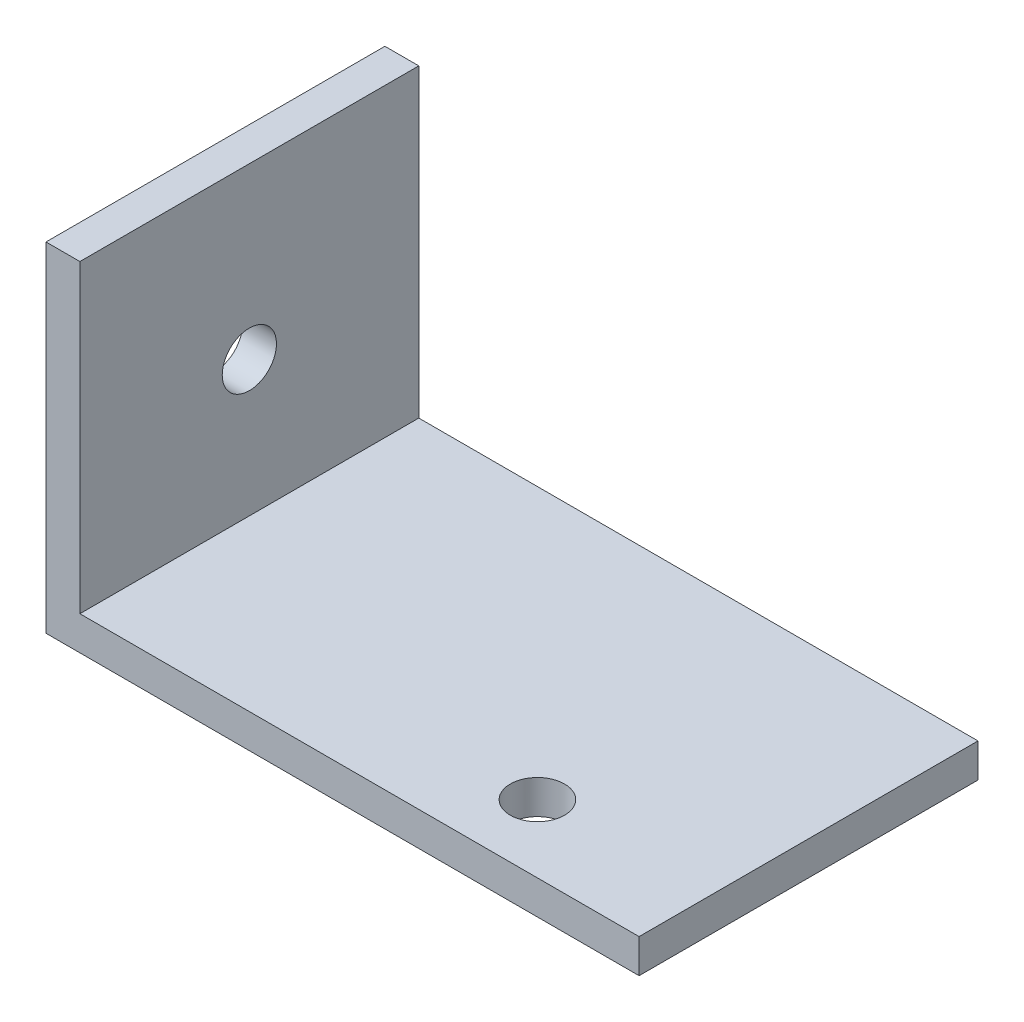
SolidWorks part; units mm, degrees
material "1060 Сплав"
ref_plane "Спереди" through (0, 0, 0) normal (0, 0, 1) x (1, 0, 0)
ref_plane "Сверху" through (0, 0, 0) normal (0, 1, 0) x (1, 0, 0)
ref_plane "Справа" through (0, 0, 0) normal (1, 0, 0) x (0, 0, -1)
sketch "Эскиз1" plane through (0, 0, 0) normal (0, 0, 1) x (1, 0, 0)
  line L0 (0, 0) -> (35, 0)
  line L1 (35, 0) -> (35, 2)
  line L2 (35, 2) -> (2, 2)
  line L3 (2, 2) -> (2, 20)
  line L4 (2, 20) -> (0, 20)
  line L5 (0, 20) -> (0, 0)
  dimension "D1" = 35
  dimension "D2" = 2
  dimension "D3" = 20
extrude "Бобышка-Вытянуть1" add sketch "Эскиз1" along normal blind 20
sketch "Эскиз3" plane through (0, 0, 0) normal (-1, 0, 0) x (0, 0, 1)
  line L0 (10, 20) -> (10, 0) construction
  line L1 (20, 20) -> (0, 20) construction
  line L2 (20, 0) -> (0, 0) construction
  line L3 (0, 10) -> (20, 10) construction
  line L4 (0, 20) -> (0, 0) construction
  line L5 (20, 20) -> (20, 0) construction
  circle A0 centre (10, 10) radius 1.6
  dimension "D1" = 3.2
extrude "Вырез-Вытянуть2" cut sketch "Эскиз3" against normal through all
sketch "Эскиз4" plane through (0, 0, 0) normal (0, -1, 0) x (1, 0, 0)
  arc A0 (23.4, 16) -> (26.6, 16) centre (25, 16) ccw construction
  arc A1 (23.4, 16) -> (26.6, 16) centre (25, 16) ccw construction
  circle A2 centre (25, 16) radius 1.6
extrude "Вырез-Вытянуть3" cut sketch "Эскиз4" against normal through all
